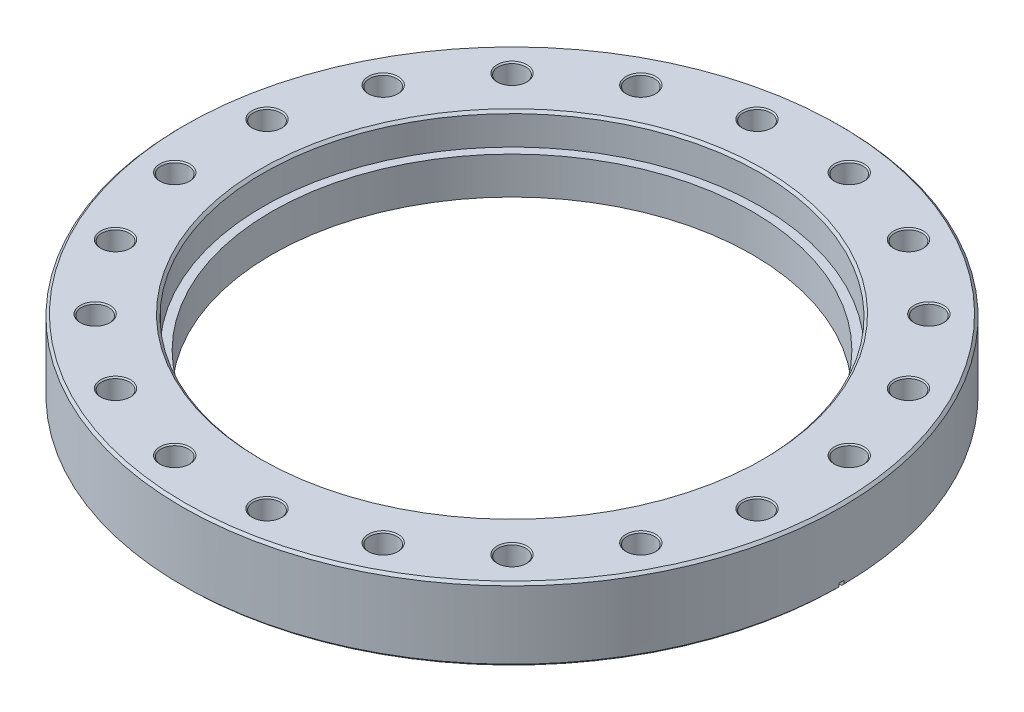
SolidWorks part; units mm, degrees
ref_plane "Front Plane" through (0, 0, 0) normal (0, 0, 1) x (1, 0, 0)
ref_plane "Top Plane" through (0, 0, 0) normal (0, 1, 0) x (1, 0, 0)
ref_plane "Right Plane" through (0, 0, 0) normal (1, 0, 0) x (0, 0, -1)
sketch "Sketch1" plane through (0, 0, 0) normal (0, 1, 0) x (1, 0, 0)
  circle A0 centre (0, 0) radius 101.219
  circle A1 centre (0, 0) radius 73.8124
  dimension "D1" = 202.438
  dimension "D2" = 147.6248
extrude "Boss-Extrude1" add sketch "Sketch1" along normal blind 22.352
sketch "Sketch2" plane through (0, 22.352, 0) normal (0, -1, 0) x (-1, 0, 0)
  circle A0 centre (0, 0) radius 76.454
  dimension "D1" = 152.908
extrude "Cut-Extrude1" cut sketch "Sketch2" along normal blind 9.652
chamfer "Chamfer1" distance 0.762 angle 45 3 edges at (0, 0, 101.219) (0, 22.352, 101.219) (0, 22.352, -76.454)
sketch "Sketch4" plane through (0, 0, 0) normal (0, 0, 1) x (1, 0, 0)
  line L0 (-85.725, 0) -> (-85.725, 1.6256)
  line L1 (-85.725, 1.6256) -> (-83.058, 0.6604)
  line L2 (-83.058, 0.6604) -> (-83.058, 1.27)
  line L3 (-83.058, 1.27) -> (0, 1.27)
  line L5 (0, 1.27) -> (0, 0)
  line L6 (0, 0) -> (-85.725, 0)
  dimension "D2" = 85.725
  dimension "D3" = 83.058
  dimension "D4" = 1.27
  dimension "D5" = 1.6256
  dimension "D6" = 0.6096
revolve "Cut-Revolve1" cut sketch "Sketch4" angle 360 about axis through (0, 22.352, 0) along (0, -1, 0)
sketch "Sketch3" plane through (0, 22.352, 0) normal (0, 1, 0) x (1, 0, 0)
  line L0 (0, 0) -> (-14.1613, 89.4111) construction
  line L1 (0, 0) -> (0, 100.457) construction
  circle A0 centre (-14.1613, 89.4111) radius 4.2164
  circle A1 centre (0, 0) radius 100.457 construction
  dimension "D2" = 8.4328
  dimension "D1" = 9
  dimension "D3" = 90.5256
extrude "Cut-Extrude2" cut sketch "Sketch3" against normal through all
chamfer "Chamfer2" distance 0.381 angle 45 2 edges at (-14.1613, 22.352, -85.1947) (-14.1613, 0, -85.1947)
pattern_circular "CirPattern1" count 20 every 18 about axis through (0, 0, 0) along (0, 1, 0) of "Cut-Extrude2", "Chamfer2"
sketch "Sketch5" plane through (0, 0, 0) normal (0, 0, 1) x (1, 0, 0)
  line L0 (-85.3543, 0.947) -> (-101.219, 1.7784)
  line L1 (-101.219, 1.7784) -> (-101.219, -3.5262)
  line L2 (-101.219, -3.5262) -> (-85.3543, -3.5262)
  line L3 (0, -3.5262) -> (-85.3543, 0.947) construction
  line L4 (-85.3543, 0.947) -> (-85.3543, -3.5262)
  line L5 (-85.3543, -3.5262) -> (0, -3.5262) construction
  line L6 (85.3543, 0.947) -> (85.3543, -3.5262)
  line L7 (101.219, -3.5262) -> (85.3543, -3.5262)
  line L8 (0, -3.5262) -> (0, 0) construction
  line L9 (101.219, 1.7784) -> (101.219, -3.5262)
  line L10 (85.3543, 0.947) -> (101.219, 1.7784)
  dimension "D1" = 3.5262
  dimension "D3" = 3
extrude "Cut-Extrude3" cut sketch "Sketch5" against normal mid plane 1.5875
